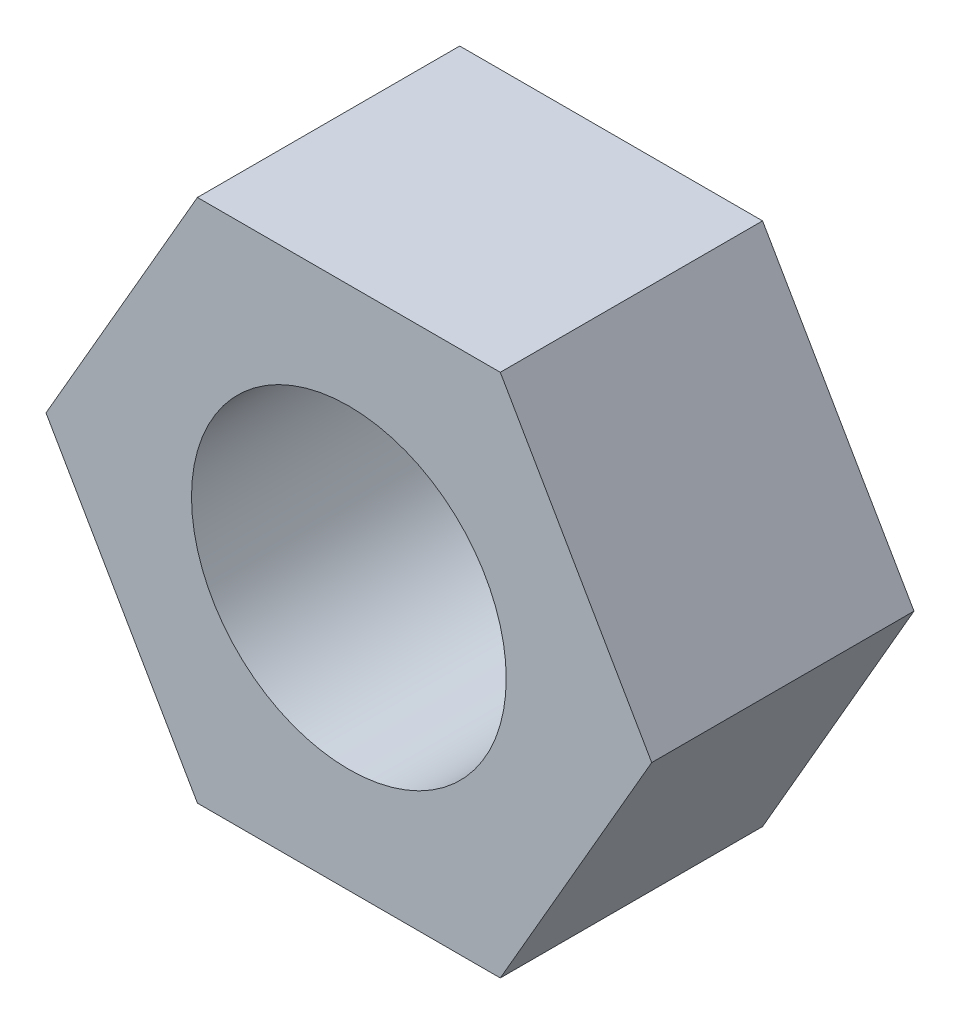
SolidWorks part; units mm, degrees
ref_plane "Plano frontal" through (0, 0, 0) normal (0, 0, 1) x (1, 0, 0)
ref_plane "Plano superior" through (0, 0, 0) normal (0, 1, 0) x (1, 0, 0)
ref_plane "Plano direito" through (0, 0, 0) normal (1, 0, 0) x (0, 0, -1)
sketch "Esboço1" plane through (0, 0, 0) normal (0, 0, 1) x (1, 0, 0)
  line L1 (2.8868, 5) -> (-2.8868, 5)
  line L2 (-2.8868, 5) -> (-5.7735, 0)
  line L3 (-5.7735, 0) -> (-2.8868, -5)
  line L4 (-2.8868, -5) -> (2.8868, -5)
  line L5 (2.8868, -5) -> (5.7735, 0)
  line L6 (5.7735, 0) -> (2.8868, 5)
  circle A0 centre (0, 0) radius 5 construction
  circle A1 centre (0, 0) radius 3
  dimension "D1" = 6
  dimension "D2" = 10
extrude "Ressalto-extrusão1" add sketch "Esboço1" along normal blind 5
